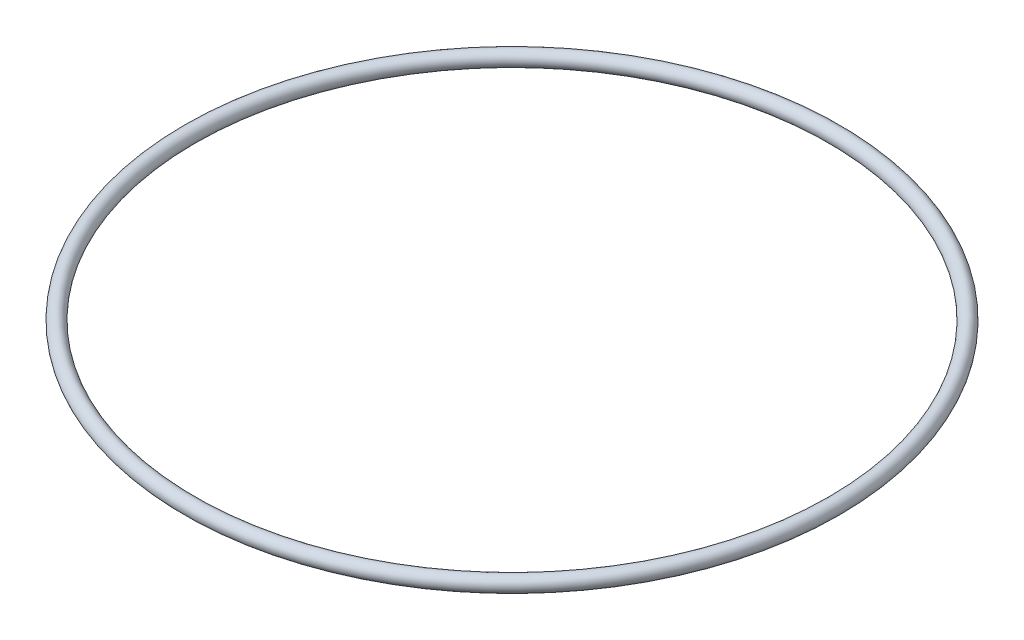
SolidWorks part; units mm, degrees
ref_plane "Front Plane" through (0, 0, 0) normal (0, 0, 1) x (1, 0, 0)
ref_plane "Top Plane" through (0, 0, 0) normal (0, 1, 0) x (1, 0, 0)
ref_plane "Right Plane" through (0, 0, 0) normal (1, 0, 0) x (0, 0, -1)
sketch "Sketch1" plane through (0, 0, 0) normal (0, 1, 0) x (1, 0, 0)
  circle A0 centre (0, 0) radius 56.3
  dimension "D1" = 112.6
sketch "Sketch2" plane through (0, 0, 0) normal (0, 0, 1) x (1, 0, 0)
  line L0 (56.3, 0) -> (-56.3, 0) construction
  circle A0 centre (-56.3, 0) radius 1.3
  dimension "D2" = 2.6
  dimension "D1" = 56.3
sweep "Sweep1" add profiles "Sketch2" path "Sketch1"
